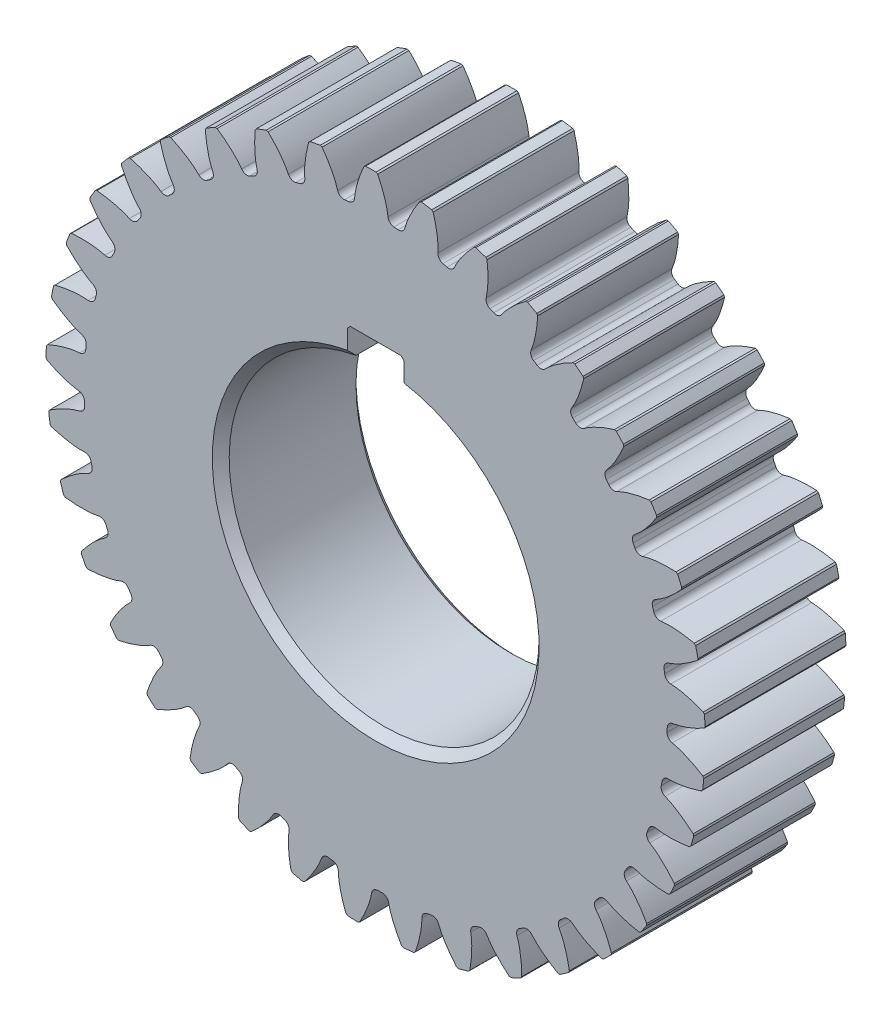
SolidWorks part; units mm, degrees
material "1.6587 (18CrNiMo7-6)"
ref_plane "Front Plane" through (0, 0, 0) normal (0, 0, 1) x (1, 0, 0)
ref_plane "Top Plane" through (0, 0, 0) normal (0, 1, 0) x (1, 0, 0)
ref_plane "Right Plane" through (0, 0, 0) normal (1, 0, 0) x (0, 0, -1)
sketch "Sketch1" plane through (0, 0, 0) normal (0, 0, 1) x (1, 0, 0)
  line L0 (0, 0) -> (0, 32.5) construction
  line L1 (5, 27.0416) -> (5, 32.5)
  line L2 (-5, 27.0416) -> (-5, 32.5)
  line L4 (5, 32.5) -> (-5, 32.5)
  line L5 (5, 0) -> (5, 32.5) construction
  line L6 (-5, 0) -> (-5, 32.5) construction
  arc A0 (-5, 27.0416) -> (5, 27.0416) centre (0, 0) ccw
  circle A1 centre (0, 0) radius 51.75
  dimension "D1" = 55
  dimension "D2" = 103.5
  dimension "D3" = 32.5
  dimension "D4" = 5
  dimension "D5" = 5
extrude "Boss-Extrude1" add sketch "Sketch1" along normal blind 25
sketch "Sketch2" plane through (0, 0, 0) normal (0, 0, 1) x (1, 0, 0)
  line L0 (0, 0) -> (55.4938, 0.8272) construction
  line L1 (0, 0) -> (66.6047, 3.8245) construction
  circle A0 centre (0, 0) radius 55.5 construction
  arc A1 (51.7394, -1.0497) -> (51.2791, 6.9651) centre (0, 0) ccw
  arc A2 (58.4578, 2.2228) -> (58.328, 4.4832) centre (0, 0) ccw
  arc A3 (52.7123, 0.0549) -> (51.7394, -1.0497) centre (52.8791, -1.0728) ccw
  arc A4 (52.3721, 5.9791) -> (51.2791, 6.9651) centre (52.4088, 7.1186) cw
  spline S0 degree 4 poles (52.1529, 0) (52.1646, 0.0001) (52.1973, 0.0009) (52.2591, 0.0041) (52.3599, 0.0116) (52.4883, 0.0247) (52.6541, 0.0456) (52.8492, 0.0753) (53.0632, 0.1133) (53.2958, 0.1604) (53.5274, 0.2125) (53.7581, 0.2692) (53.9875, 0.33) (54.2649, 0.4087) (54.5969, 0.5101) (54.9838, 0.6388) (55.4211, 0.7968) (55.8651, 0.9707) (56.3007, 1.1524) (56.7389, 1.348) (57.1616, 1.5459) (57.5987, 1.7638) (58.0012, 1.9712) (58.4497, 2.2173) (58.811, 2.4198) (59.2848, 2.7014) (59.5639, 2.872) (59.8895, 3.0767) (60.0336, 3.1702) (60.1223, 3.2278) knots 0 0 0 0 0 0.005377 0.015084 0.028532 0.04661 0.064855 0.092111 0.119476 0.146842 0.174209 0.201575 0.228941 0.256307 0.307035 0.361767 0.4165 0.471232 0.525964 0.580697 0.635429 0.690161 0.744894 0.799626 0.854358 0.909091 0.954545 1 1 1 1 1 construction
  spline S1 degree 4 poles (52.7123, 0.0549) (52.7709, 0.0636) (52.888, 0.0822) (53.0632, 0.1133) (53.2958, 0.1604) (53.5274, 0.2125) (53.7581, 0.2692) (53.9875, 0.33) (54.2649, 0.4087) (54.5969, 0.5101) (54.9838, 0.6388) (55.4211, 0.7968) (55.8651, 0.9707) (56.3007, 1.1524) (56.7389, 1.348) (57.1616, 1.5459) (57.5987, 1.7638) (57.9572, 1.9486) (58.2402, 2.1025) (58.4009, 2.1912) (58.4578, 2.2228) knots 0.064817 0.064817 0.064817 0.064817 0.064817 0.092111 0.119476 0.146842 0.174209 0.201575 0.228941 0.256307 0.307035 0.361767 0.4165 0.471232 0.525964 0.580697 0.635429 0.690161 0.744894 0.775675 0.775675 0.775675 0.775675 0.775675
  spline S2 degree 4 poles (52.3721, 5.9791) (52.4313, 5.9772) (52.5498, 5.9722) (52.7274, 5.9614) (52.9639, 5.9412) (53.1999, 5.9159) (53.4356, 5.886) (53.6704, 5.8519) (53.9551, 5.8054) (54.2964, 5.7427) (54.6955, 5.6591) (55.148, 5.5522) (55.6091, 5.4303) (56.0625, 5.2997) (56.5203, 5.1555) (56.9629, 5.0073) (57.4221, 4.8408) (57.7993, 4.6983) (58.0981, 4.5778) (58.2679, 4.508) (58.328, 4.4832) knots 0.064817 0.064817 0.064817 0.064817 0.064817 0.092111 0.119476 0.146842 0.174209 0.201575 0.228941 0.256307 0.307035 0.361767 0.4165 0.471232 0.525964 0.580697 0.635429 0.690161 0.744894 0.775675 0.775675 0.775675 0.775675 0.775675
  dimension "D1" = 111
  dimension "D2" = 103.5
  dimension "D3" = 117
  dimension "D4" = 2.28
  dimension "D5" = 2.432
extrude "Boss-Extrude2" add sketch "Sketch2" along normal blind 25
chamfer "Chamfer1" distance 0.2 2 edges at (58.4578, 2.2228, 12.5) (58.328, 4.4832, 12.5)
pattern_circular "CirPattern1" count 37 over 360 about axis through (0, 0, 25) along (0, 0, -1) of "Boss-Extrude2", "Chamfer1"
chamfer "Chamfer2" distance 1.5 1 edges at (0, -27.5, 25)
chamfer "Chamfer3" distance 1 1 edges at (0, -27.5, 0)
chamfer "Chamfer4" distance 0.5 2 edges at (5, 32.5, 12.5) (-5, 32.5, 12.5)
